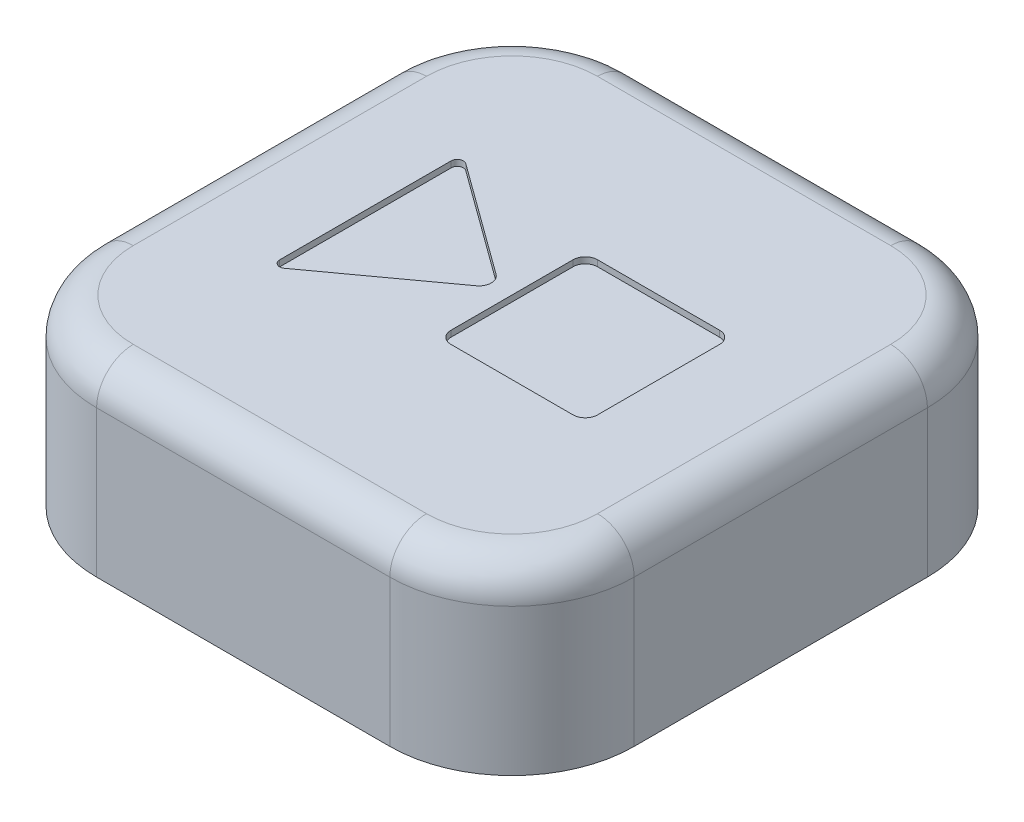
SolidWorks part; units mm, degrees
material "Acajou"
ref_plane "Plan de face" through (0, 0, 0) normal (0, 0, 1) x (1, 0, 0)
ref_plane "Plan de dessus" through (0, 0, 0) normal (0, 1, 0) x (1, 0, 0)
ref_plane "Plan de droite" through (0, 0, 0) normal (1, 0, 0) x (0, 0, -1)
sketch "Esquisse1" plane through (0, 0, 0) normal (0, 1, 0) x (1, 0, 0)
  line L1 (-12, -22) -> (12, -22)
  line L2 (-22, -12) -> (-22, 12)
  line L3 (-12, 22) -> (12, 22)
  line L4 (22, -12) -> (22, 12)
  line L5 (-22, -22) -> (22, 22) construction
  line L6 (-22, 22) -> (22, -22) construction
  arc A0 (-12, -22) -> (-22, -12) centre (-12, -12) cw
  arc A1 (12, -22) -> (22, -12) centre (12, -12) ccw
  arc A2 (12, 22) -> (22, 12) centre (12, 12) cw
  arc A3 (-22, 12) -> (-12, 22) centre (-12, 12) cw
  point P0 (0, 0)
  dimension "D3" = 10
  dimension "D1" = 44
  dimension "D2" = 44
extrude "Boss.-Extru.1" add sketch "Esquisse1" along normal blind 15
fillet "Congé1" radius 3 8 edges at (-22, 15, 0) (-19.0711, 15, -19.0711) (0, 15, -22) (19.0711, 15, -19.0711) (22, 15, 0) (19.0711, 15, 19.0711) (0, 15, 22) (-19.0711, 15, 19.0711)
sketch "Esquisse2" plane through (0, 15, 0) normal (0, 1, 0) x (1, 0, 0)
  line L0 (-12, 7.0181) -> (-12, -7.0181)
  line L1 (-11.2059, -7.4225) -> (-2.112, -0.8087)
  line L2 (-2.112, 0.8087) -> (-11.2059, 7.4225)
  line L3 (-19, 12) -> (-19, -12) construction
  line L4 (1, 6) -> (11, 6)
  line L5 (0, 5) -> (0, -5)
  line L6 (1, -6) -> (11, -6)
  line L7 (12, 5) -> (12, -5)
  line L8 (0, 6) -> (12, -6) construction
  line L9 (0, -6) -> (12, 6) construction
  line L10 (-12, 0) -> (-19, 0) construction
  line L12 (12, 0) -> (19, 0) construction
  line L14 (19, -12) -> (19, 12) construction
  arc A0 (11, -6) -> (12, -5) centre (11, -5) ccw
  arc A1 (11, 6) -> (12, 5) centre (11, 5) cw
  arc A2 (1, 6) -> (0, 5) centre (1, 5) ccw
  arc A3 (0, -5) -> (1, -6) centre (1, -5) ccw
  arc A4 (-2.112, -0.8087) -> (-2.112, 0.8087) centre (-2.7002, 0) ccw
  arc A5 (-12, -7.0181) -> (-11.2059, -7.4225) centre (-11.5, -7.0181) ccw
  arc A6 (-12, 7.0181) -> (-11.2059, 7.4225) centre (-11.5, 7.0181) cw
  point P2 (6, 0)
  point P12 (-12, 0)
  point P27 (-1, 0)
  point P30 (-12, -8)
  point P33 (-12, 8)
  point P37 (-19, 0)
  point P40 (19, 0)
  dimension "D6" = 1
  dimension "D7" = 1
  dimension "D8" = 1
  dimension "D9" = 1
  dimension "D10" = 1
  dimension "D11" = 0.5
  dimension "D12" = 0.5
  dimension "D1" = 12
  dimension "D2" = 12
  dimension "D3" = 16
  dimension "D4" = 1
  dimension "D5" = 11
extrude "Enlèv. mat.-Extru.1" cut sketch "Esquisse2" against normal blind 0.5
